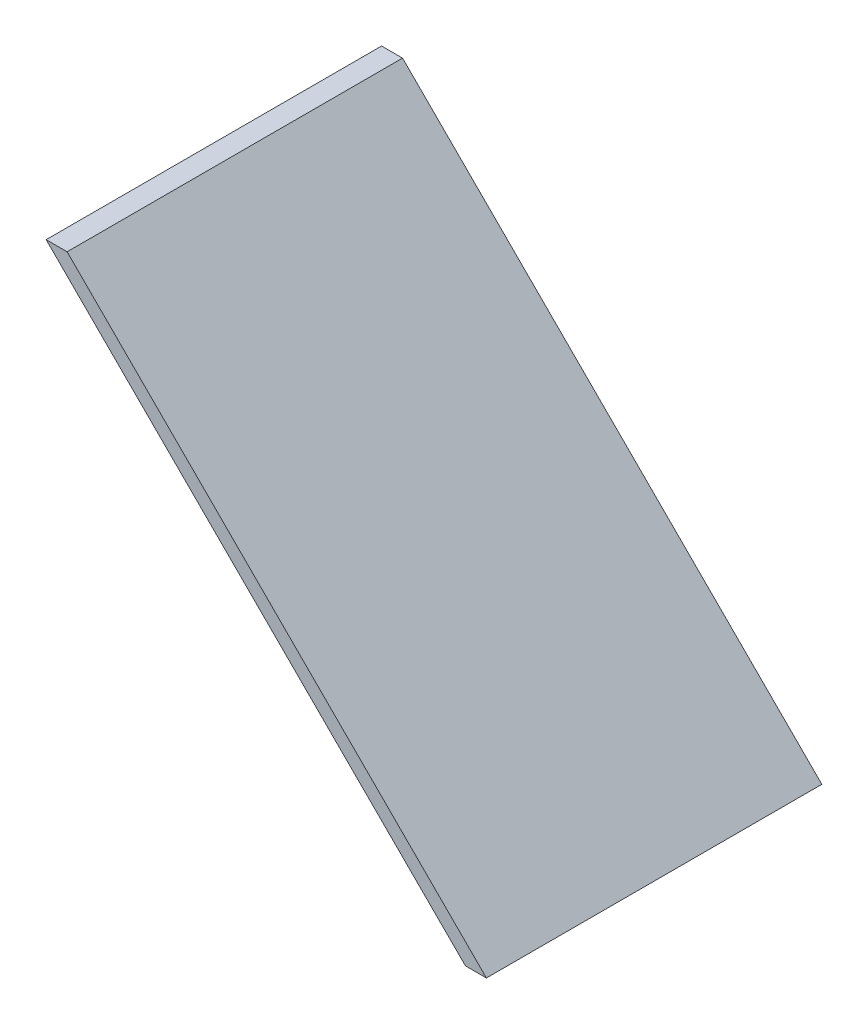
SolidWorks part; units mm, degrees
ref_plane "Front Plane" through (0, 0, 0) normal (0, 0, 1) x (1, 0, 0)
ref_plane "Top Plane" through (0, 0, 0) normal (0, 1, 0) x (1, 0, 0)
ref_plane "Right Plane" through (0, 0, 0) normal (1, 0, 0) x (0, 0, -1)
sketch "Sketch1" plane through (0, 0, 0) normal (0, 0, 1) x (1, 0, 0)
  line L0 (0, 100) -> (100, 0)
  line L1 (100, 0) -> (105, 0)
  line L3 (0, 100) -> (5, 100)
  line L5 (105, 0) -> (5, 100)
  dimension "D2" = 5
  dimension "D3" = 5
extrude "Boss-Extrude1" add sketch "Sketch1" along normal blind 80
